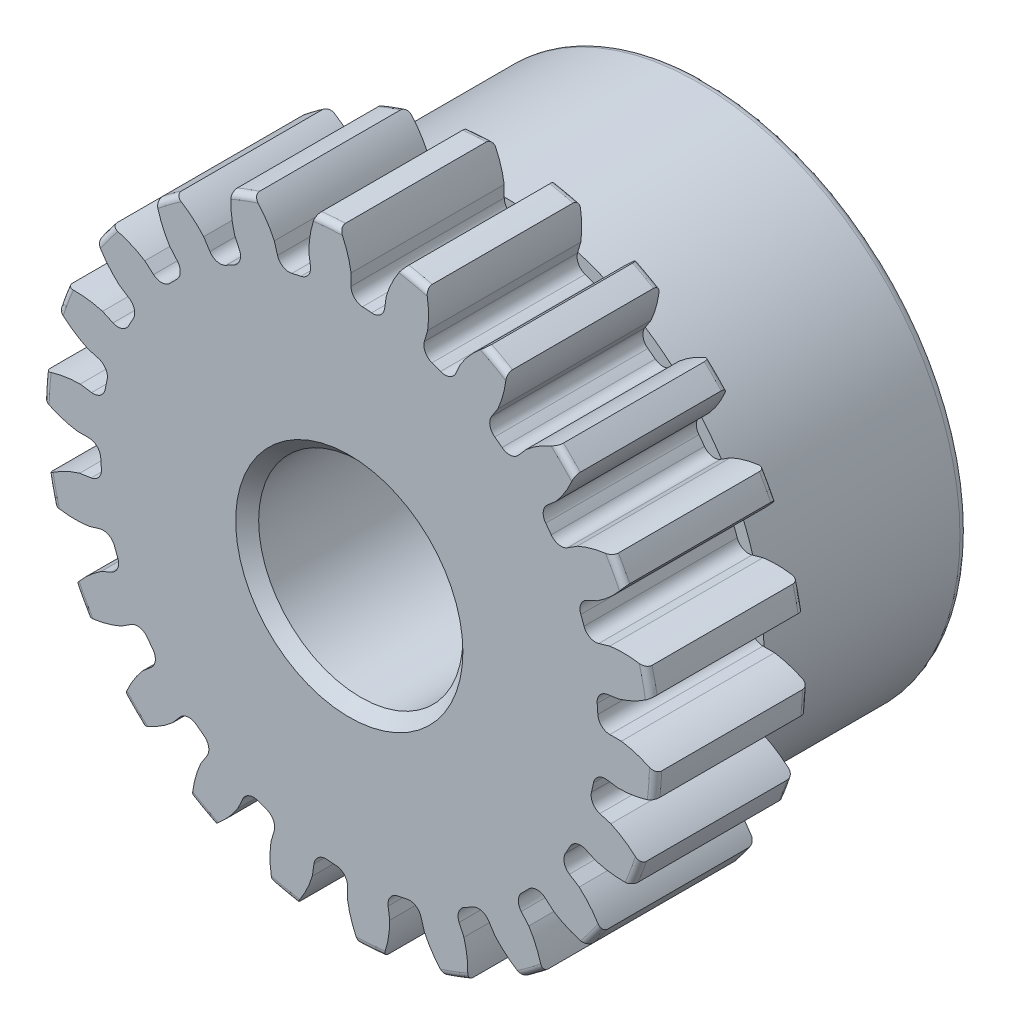
SolidWorks part; units mm, degrees
ref_plane "Front" through (0, 0, 0) normal (0, 0, 1) x (1, 0, 0)
ref_plane "Top" through (0, 0, 0) normal (0, 1, 0) x (1, 0, 0)
ref_plane "Right" through (0, 0, 0) normal (1, 0, 0) x (0, 0, -1)
sketch "Sketch1" plane through (0, 0, 0) normal (0, 0, 1) x (1, 0, 0)
  line L0 (-279.4, 0) -> (279.4, 0) construction
  circle A0 centre (0, 0) radius 9.525
  circle A1 centre (0, 0) radius 8.7376 construction
  circle A3 centre (0, 0) radius 7.7378 construction
  dimension "D3" = 0.7874
  dimension "D1" = 1.7872
extrude "Boss-Extrude1" add sketch "Sketch1" against normal blind 4.7625
sketch "Sketch2" plane through (0, 0, 0) normal (1, 0, 0) x (0, 0, -1)
  line L0 (4.7625, 0) -> (11.1125, 0)
  line L1 (4.7625, 0) -> (4.7625, 7.1438)
  line L2 (4.7625, 7.1438) -> (11.1125, 7.1437)
  line L3 (11.1125, 7.1437) -> (11.1125, 0)
  point P5 (11.1125, -7.1437)
  point P6 (0, -9.525)
  point P7 (4.7625, -9.525)
  point P9 (0, 9.525)
revolve "Revolve1" add sketch "Sketch2" angle 360 mid plane about L0
fillet "Fillet2" radius 0.1905 2 edges at (9.525, 0, -4.7625) (9.525, 0, 0)
sketch "Sketch3" plane through (0, 0, 0) normal (0, 0, 1) x (1, 0, 0)
  line L0 (0, 0) -> (0, 9.525) construction
  line L1 (-2.118, 8.1898) -> (0, 8.7376)
  line L2 (-9.5921, 8.7376) -> (9.5921, 8.7376) construction
  line L3 (-9.2865, 6.3359) -> (9.2865, 11.1393) construction
  line L4 (-2.118, 8.1898) -> (0, 0) construction
  line L5 (-5.4024, 6.5095) -> (0, 0) construction
  line L6 (-5.4024, 6.5095) -> (-0.8766, 10.2656) construction
  line L7 (-1.4769, 8.3294) -> (0, 0) construction
  line L8 (-1.4769, 8.3294) -> (0.031, 8.5967) construction
  arc A0 (-2.118, 8.1898) -> (-5.4024, 6.5095) centre (0, 0) ccw
  circle A1 centre (0, 0) radius 8.7376 construction
  circle A2 centre (0, 0) radius 8.4593 construction
  arc A3 (-2.118, 8.1898) -> (-1.4769, 8.3294) centre (0, 0) cw
  circle A4 centre (0, 0) radius 9.525 construction
  point P6 (0, 8.7376)
  dimension "D1" = 2.1877
  dimension "D3" = 5.8814
  dimension "D5" = 1.5314
  dimension "D2" = 3.7191
  dimension "D4" = 0.6563
sketch "Sketch4" plane through (0, 0, 0) normal (0, 0, 1) x (1, 0, 0)
  line L0 (0, 0) -> (0.6217, 8.6931) construction
  line L1 (0.0548, 8.4591) -> (0.0548, 7.7376)
  line L2 (0, 8.7376) -> (1.2435, 8.6487) construction
  line L3 (1.1496, 8.3808) -> (1.0469, 7.6666)
  line L4 (0.0548, 7.7376) -> (0, 0) construction
  line L5 (0, 0) -> (0, 9.525) construction
  line L6 (-5.4024, 6.5095) -> (-0.8766, 10.2656) construction
  line L7 (-5.4024, 6.5095) -> (-0.8766, 10.2656) construction
  arc A0 (1.0469, 7.6666) -> (0.0548, 7.7376) centre (0, 0) ccw
  arc A1 (0, 8.7376) -> (1.2435, 8.6487) centre (0, 0) cw construction
  circle A2 centre (0, 0) radius 8.7376 construction
  circle A3 centre (0, 0) radius 8.4593 construction
  circle A4 centre (0, 0) radius 7.7378 construction
  arc A5 (2.3286, 10.0364) -> (-0.8766, 10.2656) centre (0, 0) ccw
  spline S0 degree 2 poles (-0.8766, 10.2656) (-0.0977, 9.4713) (0.0548, 8.4591) knots 0 0 0 1 1 1
  spline S1 degree 2 poles (2.3286, 10.0364) (1.4446, 9.361) (1.1496, 8.3808) knots 0 0 0 1 1 1
  dimension "D1" = 1.2477
extrude "Cut-Extrude1" cut sketch "Sketch4" against normal through all
fillet "Fillet1" radius 0.3743 2 edges at (1.0469, 7.6666, -2.3813) (0.0548, 7.7376, -2.3813)
pattern_circular "CirPattern1" count 22 over 360 about axis through (0, 0, -4.7625) along (0, 0, 1) of "Cut-Extrude1", "Fillet1"
sketch "Sketch5" plane through (0, 0, 0) normal (0, 0, 1) x (1, 0, 0)
  circle A0 centre (0, 0) radius 3.175
  circle A1 centre (0, 0) radius 1.5875 construction
  dimension "Bore Min" = 6.35
  dimension "Bore Max" = 3.175
extrude "Cut-Extrude2" cut sketch "Sketch5" against normal through all
chamfer "Chamfer1" distance 0.3572 angle 45 3 edges at (7.1437, 0, -11.1125) (3.175, 0, 0) (3.175, 0, -11.1125)
sketch "Pitch Dia" plane through (0, 0, 0) normal (0, 0, 1) x (1, 0, 0)
  circle A0 centre (0, 0) radius 8.7376 construction
  circle A1 centre (0, 0) radius 8.7376 construction
sketch "Sketch6" plane through (0, 0, -4.7625) normal (0, 0, -1) x (-1, 0, 0)
  circle A0 centre (0, 0) radius 8.128
  dimension "D1" = 16.256
extrude "Boss-Extrude2" add sketch "Sketch6" along normal blind 6.35
fillet "Fillet3" radius 0.254 1 edges at (-8.128, 0, -11.1125)
equation "\"D1@Boss-Extrude1\" = \"Face Wd@Sketch2\""
equation "\"D2@Sketch3\" = \"D1@Sketch3\"*1.7"
equation "\"D3@Sketch3\" = \"D1@Sketch3\"+\"D2@Sketch3\"-.001"
equation "\"D4@Sketch3\" = \"D1@Sketch3\"*.3"
equation "\"D5@Sketch3\" = \"D1@Sketch3\"-\"D4@Sketch3\""
equation "\"D1@Sketch4\" = 1.5708/(\"Number of Teeth@Sketch1\"/\"Ptich Dia@Sketch1\")"
equation "\"D1@Chamfer1\" = \"B Hub Dia@Sketch2\"*.025"
equation "\"D1@CirPattern1\" = \"Number of Teeth@Sketch1\""
equation "\"D1@Fillet1\" = \"D1@Sketch4\"*.3"
equation "\"D1@Fillet2\" = \"OD@Sketch1\"*.01"
equation "\"D1@Sketch1\" = 2.250/(\"Number of Teeth@Sketch1\"/\"Ptich Dia@Sketch1\")"
